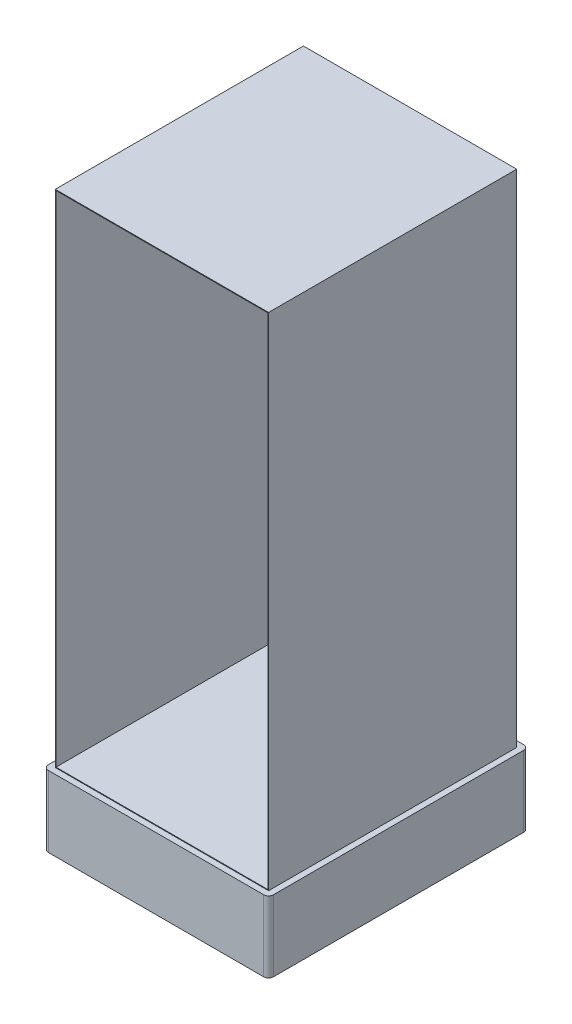
SolidWorks part; units mm, degrees
ref_plane "Alzado" through (0, 0, 0) normal (0, 0, 1) x (1, 0, 0)
ref_plane "Planta" through (0, 0, 0) normal (0, 1, 0) x (1, 0, 0)
ref_plane "Vista lateral" through (0, 0, 0) normal (1, 0, 0) x (0, 0, -1)
sketch "Croquis1" plane through (0, 0, 0) normal (0, 1, 0) x (1, 0, 0)
  line L1 (-450, 523.5) -> (450, 523.5)
  line L2 (-450, 523.5) -> (-450, -523.5)
  line L3 (-450, -523.5) -> (450, -523.5)
  line L4 (450, 523.5) -> (450, -523.5)
  line L5 (-450, 523.5) -> (450, -523.5) construction
  line L6 (-450, -523.5) -> (450, 523.5) construction
  point P0 (0, 0)
  dimension "D1" = 1047
  dimension "D2" = 900
extrude "Saliente-Extruir1" add sketch "Croquis1" along normal blind 2113
shell "Vaciado2" thickness 10
sketch "Croquis2" plane through (0, 0, 523.5) normal (0, 0, 1) x (1, 0, 0)
  line L0 (-440, 2103) -> (440, 2103)
  line L1 (440, 2103) -> (440, 10)
  line L2 (440, 10) -> (-440, 10)
  line L3 (-440, 10) -> (-440, 2103)
extrude "Saliente-Extruir2" add sketch "Croquis2" against normal blind 5
sketch "Croquis4" plane through (0, 0, 0) normal (0, -1, 0) x (1, 0, 0)
  line L0 (-450, -523.5) -> (-450, 523.5) construction
  line L1 (-454.3565, 548.5) -> (454.3565, 548.5)
  line L2 (-475, 527.8565) -> (-475, -527.8565)
  line L3 (-454.3565, -548.5) -> (454.3565, -548.5)
  line L4 (475, 527.8565) -> (475, -527.8565)
  line L5 (-475, 548.5) -> (475, -548.5) construction
  line L6 (-475, -548.5) -> (475, 548.5) construction
  line L7 (-450, 523.5) -> (450, 523.5) construction
  arc A0 (454.3565, 548.5) -> (475, 527.8565) centre (454.3565, 527.8565) cw
  arc A1 (454.3565, -548.5) -> (475, -527.8565) centre (454.3565, -527.8565) ccw
  arc A2 (-475, -527.8565) -> (-454.3565, -548.5) centre (-454.3565, -527.8565) ccw
  arc A3 (-454.3565, 548.5) -> (-475, 527.8565) centre (-454.3565, 527.8565) ccw
  point P0 (0, 0)
  dimension "D3" = 20.6435
  dimension "D1" = 25
  dimension "D2" = 25
extrude "Saliente-Extruir3" add sketch "Croquis4" along normal blind 300
sketch "Croquis5" plane through (0, 0, -513.5) normal (0, 0, 1) x (1, 0, 0)
  line L0 (-447, 10) -> (-447, 2110)
  line L1 (-447, 2110) -> (447, 2110)
  line L2 (447, 2110) -> (447, 10)
  line L3 (440, 10) -> (-440, 10) construction
  line L4 (-447, 10) -> (-447, 3)
  line L5 (-450, 2113) -> (-450, 0) construction
  line L7 (-447, 3) -> (447, 3)
  line L8 (447, 3) -> (447, 10)
  line L9 (450, 0) -> (-450, 0) construction
  line L10 (450, 2113) -> (450, 0) construction
  line L11 (-450, 2113) -> (450, 2113) construction
  dimension "D1" = 3
  dimension "D2" = 3
  dimension "D3" = 3
  dimension "D4" = 3
extrude "Cortar-Extruir1" cut sketch "Croquis5" along normal blind 1044
